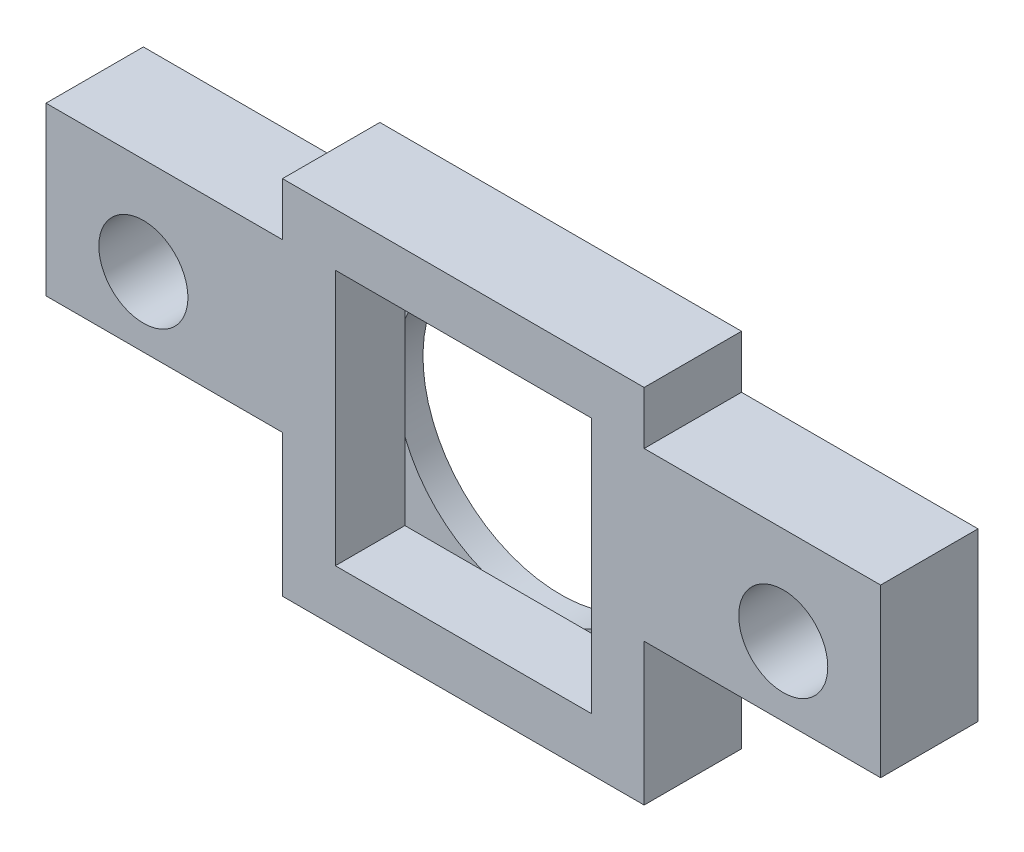
SolidWorks part; units mm, degrees
ref_plane "前视基准面" through (0, 0, 0) normal (0, 0, 1) x (1, 0, 0)
ref_plane "上视基准面" through (0, 0, 0) normal (0, 1, 0) x (1, 0, 0)
ref_plane "右视基准面" through (0, 0, 0) normal (1, 0, 0) x (0, 0, -1)
sketch "草图1" plane through (0, 0, 0) normal (0, 0, 1) x (1, 0, 0)
  line L1 (-7.0658, 7.596) -> (5.9342, 7.596)
  line L2 (-7.0658, 7.596) -> (-7.0658, -5.404)
  line L3 (-7.0658, -5.404) -> (5.9342, -5.404)
  line L4 (5.9342, 7.596) -> (5.9342, -5.404)
  circle A0 centre (-0.5658, 1.096) radius 4.95
  dimension "D1" = 9.9
  dimension "D2" = 6.5
  dimension "D3" = 6.5
  dimension "D4" = 13
  dimension "D5" = 13
extrude "凸台-拉伸1" add sketch "草图1" along normal blind 1
sketch "草图2" plane through (0, 0, 1) normal (0, 0, 1) x (1, 0, 0)
  line L1 (-7.0658, 7.596) -> (5.9342, 7.596)
  line L2 (-7.0658, 7.596) -> (-7.0658, -5.404)
  line L3 (-7.0658, -5.404) -> (5.9342, -5.404)
  line L4 (5.9342, 7.596) -> (5.9342, -5.404)
  line L5 (-5.1658, 5.696) -> (4.0342, 5.696)
  line L6 (-5.1658, 5.696) -> (-5.1658, -3.504)
  line L7 (-5.1658, -3.504) -> (4.0342, -3.504)
  line L8 (4.0342, 5.696) -> (4.0342, -3.504)
  circle A0 centre (-0.5658, 1.096) radius 4.6 construction
  dimension "D1" = 9.2
  dimension "D2" = 9.2
  dimension "D3" = 9.2
extrude "凸台-拉伸2" add sketch "草图2" along normal blind 2.5
sketch "草图3" plane through (0, 0, 3.5) normal (0, 0, 1) x (1, 0, 0)
  line L0 (-0.5658, 7.596) -> (-0.5658, -5.404) construction
  line L1 (5.9342, 5.696) -> (14.4342, 5.696)
  line L2 (5.9342, 5.696) -> (5.9342, -0.304)
  line L3 (5.9342, -0.304) -> (14.4342, -0.304)
  line L4 (14.4342, 5.696) -> (14.4342, -0.304)
  line L5 (5.9342, 7.596) -> (-7.0658, 7.596) construction
  line L6 (-7.0658, -5.404) -> (5.9342, -5.404) construction
  line L7 (-15.5658, 5.696) -> (-15.5658, -0.304)
  line L8 (-7.0658, -0.304) -> (-15.5658, -0.304)
  line L9 (-7.0658, 5.696) -> (-7.0658, -0.304)
  line L10 (-7.0658, 5.696) -> (-15.5658, 5.696)
  line L11 (4.0342, 5.696) -> (-5.1658, 5.696) construction
  circle A0 centre (10.9342, 2.196) radius 1.6
  circle A1 centre (-12.0658, 2.196) radius 1.6
  dimension "D2" = 3.2
  dimension "D3" = 3.5
  dimension "D4" = 3.5
  dimension "D1" = 15
  dimension "D5" = 6
extrude "凸台-拉伸3" add sketch "草图3" against normal blind 3.5
